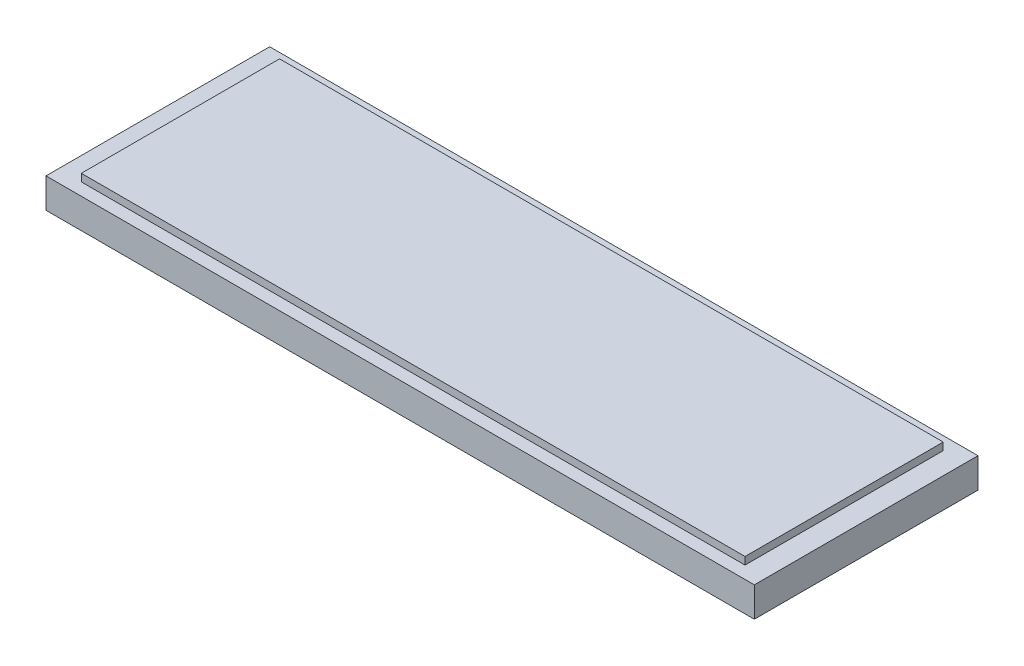
SolidWorks part; units mm, degrees
ref_plane "Front Plane" through (0, 0, 0) normal (0, 0, 1) x (1, 0, 0)
ref_plane "Top Plane" through (0, 0, 0) normal (0, 1, 0) x (1, 0, 0)
ref_plane "Right Plane" through (0, 0, 0) normal (1, 0, 0) x (0, 0, -1)
sketch "Sketch1" plane through (0, 0, 0) normal (0, 1, 0) x (1, 0, 0)
  line L1 (-103.0508, 43.02) -> (86.9492, 43.02)
  line L2 (-103.0508, 43.02) -> (-103.0508, -16.98)
  line L3 (-103.0508, -16.98) -> (86.9492, -16.98)
  line L4 (86.9492, 43.02) -> (86.9492, -16.98)
  dimension "D1" = 190
  dimension "D2" = 60
extrude "Boss-Extrude1" add sketch "Sketch1" along normal blind 8
sketch "Sketch2" plane through (0, 8, 0) normal (0, 1, 0) x (1, 0, 0)
  line L1 (-96.9141, 39.5284) -> (81.1136, 39.5284)
  line L2 (-96.9141, 39.5284) -> (-96.9141, -13.6389)
  line L3 (-96.9141, -13.6389) -> (81.1136, -13.6389)
  line L4 (81.1136, 39.5284) -> (81.1136, -13.6389)
extrude "Boss-Extrude2" add sketch "Sketch2" along normal blind 2
